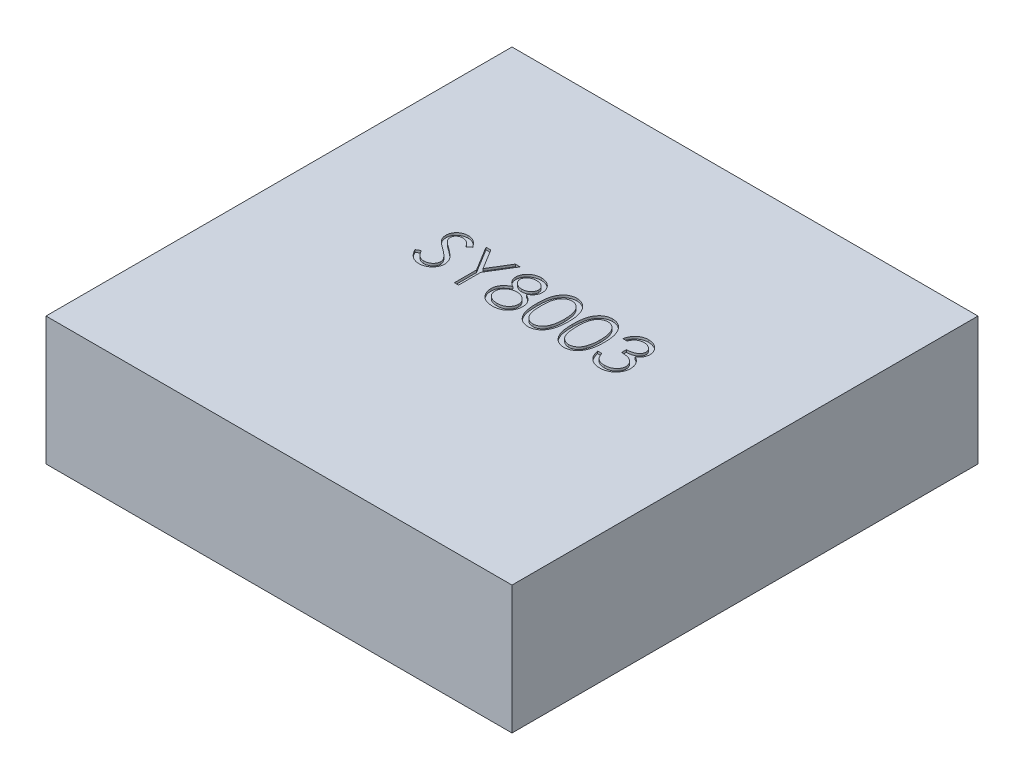
SolidWorks part; units mm, degrees
ref_plane "Front Plane" through (0, 0, 0) normal (0, 0, 1) x (1, 0, 0)
ref_plane "Top Plane" through (0, 0, 0) normal (0, 1, 0) x (1, 0, 0)
ref_plane "Right Plane" through (0, 0, 0) normal (1, 0, 0) x (0, 0, -1)
sketch "BaseS" plane through (0, 0, 0) normal (0, 1, 0) x (1, 0, 0)
  line L1 (-1, 1) -> (1, 1)
  line L2 (-1, 1) -> (-1, -1)
  line L3 (-1, -1) -> (1, -1)
  line L4 (1, 1) -> (1, -1)
  line L5 (-1, 1) -> (1, -1) construction
  line L6 (-1, -1) -> (1, 1) construction
  point P0 (0, 0)
  dimension "Dim" = 2
extrude "Base" add sketch "BaseS" along normal blind 0.55
sketch "PartNumberS" plane through (0, 0.55, 0) normal (0, 1, 0) x (1, 0, 0)
  line L0 (1, 0) -> (-1, 0) construction
  line L4 (-1, 1) -> (-1, -1) construction
  line L5 (1, -1) -> (1, 1) construction
  text T0 "SY8003" font "Century Gothic" height 0.2
  point P2 (-0.8315, 1.5)
  point P4 (-1, 1.5)
  point P6 (1, 0)
extrude "PartNumber" cut sketch "PartNumberS" against normal blind 0.01
